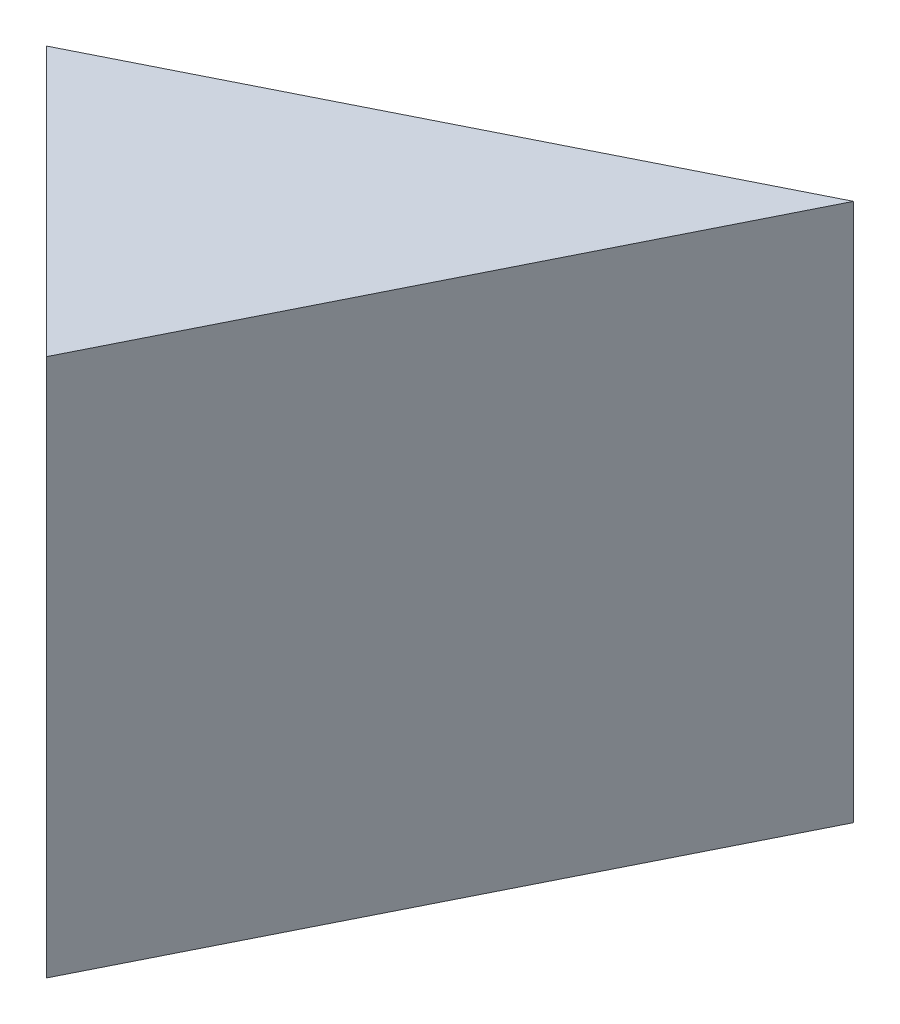
SolidWorks part; units mm, degrees
ref_plane "Front Plane" through (0, 0, 0) normal (0, 0, 1) x (1, 0, 0)
ref_plane "Top Plane" through (0, 0, 0) normal (0, 1, 0) x (1, 0, 0)
ref_plane "Right Plane" through (0, 0, 0) normal (1, 0, 0) x (0, 0, -1)
sketch "Sketch1" plane through (0, 0, 0) normal (0, 0, 1) x (1, 0, 0)
  line L1 (0, 0) -> (20, 0)
  line L2 (0, 0) -> (0, 20)
  line L3 (0, 20) -> (20, 20)
  line L4 (20, 0) -> (20, 20)
  dimension "D1" = 20
  dimension "D2" = 20
extrude "Boss-Extrude1" add sketch "Sketch1" along normal blind 20
sketch "Sketch2" plane through (0, 20, 0) normal (0, 1, 0) x (1, 0, 0)
  line L0 (20, 0) -> (10, -20)
  line L1 (20, -20) -> (0, -20) construction
  line L2 (10, -20) -> (20, -20)
  line L3 (20, -20) -> (20, 0)
extrude "Cut-Extrude1" cut sketch "Sketch2" against normal blind 20
sketch "Sketch3" plane through (0, 20, 0) normal (0, 1, 0) x (1, 0, 0)
  line L0 (0, -20) -> (10, -20)
  line L1 (10, -20) -> (0, -10)
  line L2 (0, -20) -> (0, 0) construction
  line L3 (0, -10) -> (0, -20)
extrude "Cut-Extrude2" cut sketch "Sketch3" against normal blind 20
sketch "Sketch4" plane through (0, 20, 0) normal (0, 1, 0) x (1, 0, 0)
  line L0 (20, 0) -> (0, -10)
  line L1 (0, -10) -> (0, 0)
  line L2 (0, 0) -> (20, 0)
extrude "Cut-Extrude3" cut sketch "Sketch4" against normal blind 20
